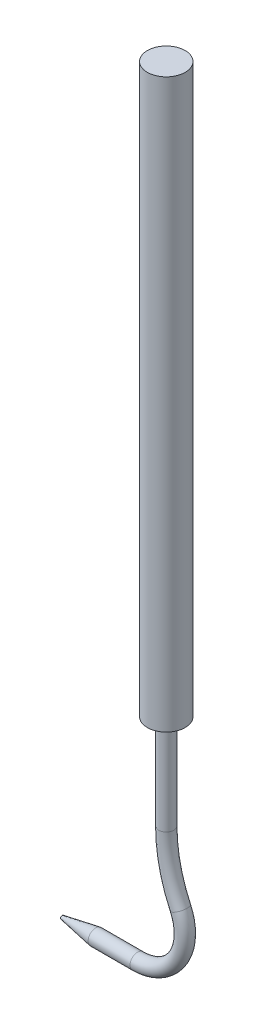
SolidWorks part; units mm, degrees
material "Copper"
ref_plane "Front Plane" through (0, 0, 0) normal (0, 0, 1) x (1, 0, 0)
ref_plane "Top Plane" through (0, 0, 0) normal (0, 1, 0) x (1, 0, 0)
ref_plane "Right Plane" through (0, 0, 0) normal (1, 0, 0) x (0, 0, -1)
sketch "Sketch1" plane through (0, 0, 0) normal (0, 0, 1) x (1, 0, 0)
  line L0 (0, 0) -> (0, 28.4693) construction
  line L1 (0, 0) -> (3, 0)
  line L2 (0, 0) -> (2.2685, -0.4)
  line L3 (2.2685, -0.4) -> (3, -0.4)
  line L4 (3, 0) -> (3, -0.4)
  line L5 (0, 0) -> (-76.4546, 0) construction
  dimension "D1" = 0.8
  dimension "D2" = 3
  dimension "D3" = 10
revolve "Revolve1" add sketch "Sketch1" angle 360 about L5
sketch "Sketch2" plane through (0, 0, 0) normal (0, 1, 0) x (1, 0, 0)
  circle A0 centre (0, 0) radius 0.5
  dimension "D1" = 1
extrude "Cut-Extrude1" cut sketch "Sketch2" against normal through all and the other way through all
sketch "Sketch3" plane through (3, 0, 0) normal (1, 0, 0) x (0, 0, -1)
  circle A0 centre (0, 0) radius 0.4
  circle A1 centre (0, 0) radius 0.4 construction
sketch "Sketch4" plane through (0, 0, 0) normal (0, 0, 1) x (1, 0, 0)
  line L0 (3, 0) -> (4.4838, 0)
  line L1 (6, 6.9375) -> (6, 11.9375)
  line L2 (6.7495, 3.5565) -> (4.4838, 2.5) construction
  line L3 (4.4838, 2.5) -> (4.4838, 0) construction
  line L4 (6, 11.9375) -> (5, 11.9375) construction
  line L5 (5, 2.6) -> (5, 41.4) construction
  arc A0 (4.4838, 0) -> (6.7495, 3.5565) centre (4.4838, 2.5) ccw
  arc A1 (6.7495, 3.5565) -> (6, 6.9375) centre (14, 6.9375) cw
  dimension "D2" = 2.5
  dimension "D3" = 8
  dimension "D1" = 1
  dimension "D4" = 5
  dimension "D5" = 115
sweep "Sweep1" add profiles "Sketch3" path "Sketch4"
sketch "Sketch5" plane through (0, 11.9375, 0) normal (0, 1, 0) x (-1, 0, 0)
  line L0 (-6.4, 0) -> (-7, 0) construction
  circle A0 centre (-6, 0) radius 1
  circle A1 centre (-6, 0) radius 0.4 construction
  circle A2 centre (-6, 0) radius 0.4 construction
  dimension "D1" = 0.6
extrude "Boss-Extrude1" add sketch "Sketch5" along normal blind 30
